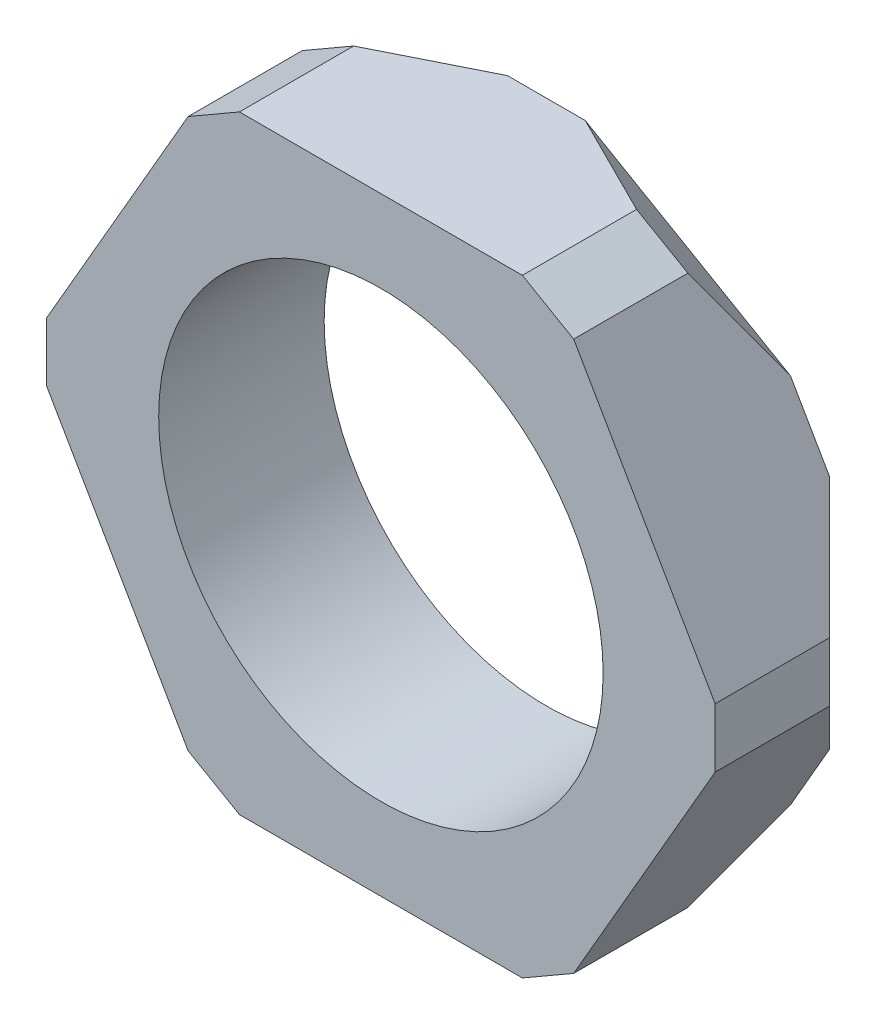
SolidWorks part; units mm, degrees
ref_plane "Front Plane" through (0, 0, 0) normal (0, 0, 1) x (1, 0, 0)
ref_plane "Top Plane" through (0, 0, 0) normal (0, 1, 0) x (1, 0, 0)
ref_plane "Right Plane" through (0, 0, 0) normal (1, 0, 0) x (0, 0, -1)
sketch "Sketch1" plane through (0, 0, 0) normal (0, 0, 1) x (1, 0, 0)
  line L1 (5.1384, 8.9) -> (-5.1384, 8.9)
  line L2 (-5.1384, 8.9) -> (-10.2768, 0)
  line L3 (-10.2768, 0) -> (-5.1384, -8.9)
  line L4 (-5.1384, -8.9) -> (5.1384, -8.9)
  line L5 (5.1384, -8.9) -> (10.2768, 0)
  line L6 (10.2768, 0) -> (5.1384, 8.9)
  circle A0 centre (0, 0) radius 6.5
  circle A1 centre (0, 0) radius 8.9 construction
  dimension "D1" = 13
  dimension "D2" = 17.8
extrude "Boss-Extrude1" add sketch "Sketch1" along normal blind 4.84
chamfer "Chamfer1" distance 1 6 edges at (5.1384, -8.9, 2.42) (-5.1384, -8.9, 2.42) (-10.2768, 0, 2.42) (-5.1384, 8.9, 2.42) (10.2768, 0, 2.42) (5.1384, 8.9, 2.42)
chamfer "Chamfer2" distance 1.5 angle 45 6 edges at (-4.8884, 8.467, 0) (-9.7768, 0, 0) (-4.8884, -8.467, 0) (4.8884, -8.467, 0) (9.7768, 0, 0) (4.8884, 8.467, 0)
